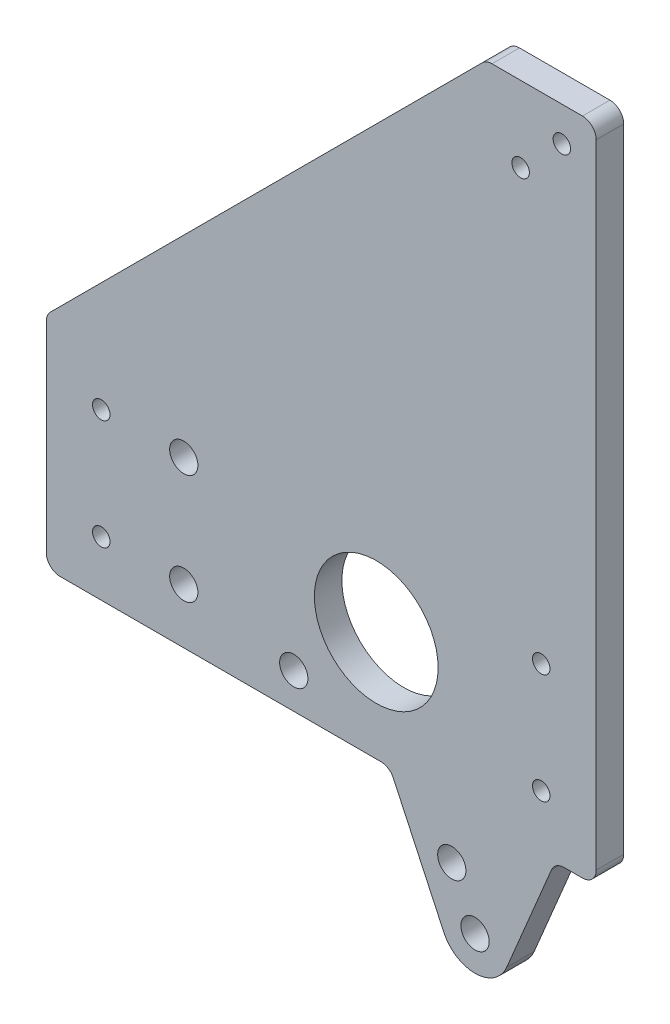
SolidWorks part; units mm, degrees
material "6061 Alloy"
ref_plane "Front Plane" through (0, 0, 0) normal (0, 0, 1) x (1, 0, 0)
ref_plane "Top Plane" through (0, 0, 0) normal (0, 1, 0) x (1, 0, 0)
ref_plane "Right Plane" through (0, 0, 0) normal (1, 0, 0) x (0, 0, -1)
sketch "Sketch1" plane through (0, 0, 0) normal (0, 0, 1) x (1, 0, 0)
  line L0 (-12.7, -76.2) -> (-26.2558, -76.2) construction
  line L1 (-12.7, -76.2) -> (12.7, -76.2) construction
  line L2 (-12.7, -76.2) -> (-12.7, 76.2) construction
  line L3 (-12.7, 76.2) -> (12.7, 76.2)
  line L4 (12.7, -76.2) -> (12.7, 76.2)
  line L5 (-12.7, -76.2) -> (12.7, 76.2) construction
  line L6 (-12.7, 76.2) -> (12.7, -76.2) construction
  line L7 (-114.3, -76.2) -> (-114.3, -25.4)
  line L8 (-12.7, 76.2) -> (-114.3, -25.4)
  line L9 (-38.1, -76.2) -> (-38.1, -50.8) construction
  line L10 (-38.1, -50.8) -> (12.7, -50.8) construction
  line L11 (-38.1, -50.8) -> (-15.2892, -99.718) construction
  line L12 (12.7, -76.2) -> (-7.9687, -102.7863) construction
  line L13 (-22.483, -103.0725) -> (-35.0138, -76.2)
  line L14 (-35.0138, -76.2) -> (-114.3, -76.2)
  line L15 (-7.9687, -102.7863) -> (3.175, -76.2)
  line L16 (3.175, -76.2) -> (12.7, -76.2)
  circle A0 centre (-15.2892, -99.718) radius 3.2639
  circle A1 centre (-20.6564, -88.2079) radius 3.2639
  arc A2 (-7.9687, -102.7863) -> (-22.483, -103.0725) centre (-15.2892, -99.718) cw
  point P0 (0, 0)
  dimension "D9" = 12.7
  dimension "D10" = 6.5278
  dimension "D11" = 6.5278
  dimension "D12" = 7.9375
  dimension "D1" = 25.4
  dimension "D2" = 152.4
  dimension "D3" = 101.6
  dimension "D4" = 50.8
  dimension "D5" = 25.4
  dimension "D6" = 50.8
  dimension "D7" = 65
  dimension "D8" = 53.975
  dimension "D13" = 65
  dimension "D14" = 9.525
extrude "Boss-Extrude1" add sketch "Sketch1" along normal blind 6.35
sketch "Sketch2" plane through (0, 0, 6.35) normal (0, 0, 1) x (1, 0, 0)
  line L1 (12.7, 76.2) -> (4.7625, 76.2) construction
  line L2 (12.7, 76.2) -> (12.7, 68.2625) construction
  line L3 (12.7, 68.2625) -> (4.7625, 68.2625) construction
  line L4 (4.7625, 76.2) -> (4.7625, 68.2625) construction
  line L5 (12.7, 76.2) -> (-4.7625, 76.2) construction
  line L6 (12.7, 76.2) -> (12.7, 58.7375) construction
  line L7 (12.7, 58.7375) -> (-4.7625, 58.7375) construction
  line L8 (-4.7625, 76.2) -> (-4.7625, 58.7375) construction
  circle A0 centre (4.7625, 68.2625) radius 2.0193
  circle A1 centre (-4.7625, 58.7375) radius 2.0193
  dimension "D3" = 4.0386
  dimension "D6" = 4.0386
  dimension "D1" = 7.9375
  dimension "D2" = 7.9375
  dimension "D4" = 17.4625
  dimension "D5" = 17.4625
extrude "Cut-Extrude1" cut sketch "Sketch2" against normal blind 6.35
sketch "Sketch3" plane through (0, 0, 6.35) normal (0, 0, 1) x (1, 0, 0)
  line L0 (0, -63.5) -> (0, -38.1) construction
  line L1 (12.7, -76.2) -> (0, -76.2) construction
  line L2 (12.7, -76.2) -> (12.7, -63.5) construction
  line L3 (12.7, -63.5) -> (0, -63.5) construction
  line L4 (0, -76.2) -> (0, -63.5) construction
  circle A0 centre (0, -63.5) radius 2.0193
  circle A1 centre (0, -38.1) radius 2.0193
  dimension "D3" = 4.0386
  dimension "D5" = 4.0386
  dimension "D1" = 12.7
  dimension "D2" = 12.7
  dimension "D4" = 25.4
extrude "Cut-Extrude2" cut sketch "Sketch3" against normal blind 6.35
sketch "Sketch5" plane through (0, 0, 6.35) normal (0, 0, 1) x (1, 0, 0)
  line L0 (-101.6, -63.5) -> (-101.6, -38.1) construction
  line L1 (-114.3, -76.2) -> (-101.6, -76.2) construction
  line L2 (-114.3, -76.2) -> (-114.3, -63.5) construction
  line L3 (-114.3, -63.5) -> (-101.6, -63.5) construction
  line L4 (-101.6, -76.2) -> (-101.6, -63.5) construction
  circle A0 centre (-101.6, -63.5) radius 2.0193
  circle A1 centre (-101.6, -38.1) radius 2.0193
  dimension "D3" = 4.0386
  dimension "D5" = 4.0386
  dimension "D1" = 12.7
  dimension "D2" = 12.7
  dimension "D4" = 25.4
extrude "Cut-Extrude3" cut sketch "Sketch5" against normal blind 6.35
sketch "Sketch6" plane through (0, 0, 6.35) normal (0, 0, 1) x (1, 0, 0)
  line L0 (12.7, -76.2) -> (12.7, 76.2) construction
  line L2 (-114.3, -76.2) -> (-35.0138, -76.2) construction
  circle A0 centre (-38.1, -50.8) radius 14.2875
  dimension "D3" = 28.575
  dimension "D2" = 25.4
  dimension "D1" = 50.8
extrude "Cut-Extrude4" cut sketch "Sketch6" against normal through all
sketch "Sketch7" plane through (0, 0, 6.35) normal (0, 0, 1) x (1, 0, 0)
  line L0 (-38.1, -50.8) -> (-57.15, -50.8) construction
  line L1 (-57.15, -50.8) -> (-57.15, -64.77) construction
  line L2 (-57.15, -68.0339) -> (-57.15, -64.77) construction
  circle A0 centre (-57.15, -68.0339) radius 3.2639
  dimension "D3" = 6.5278
  dimension "D1" = 19.05
  dimension "D2" = 13.97
extrude "Cut-Extrude5" cut sketch "Sketch7" against normal through all
hole_wizard "F (0.257) Diameter Hole1" positions "Sketch8" profile "Sketch9" hole size "F" standard "ANSI Inch" end condition through all
sketch "Sketch8" plane through (0, 0, 6.35) normal (0, 0, 1) x (1, 0, 0)
  line L1 (-114.3, -25.4) -> (-114.3, -76.2) construction
  line L2 (-114.3, -76.2) -> (-35.0138, -76.2) construction
  point P0 (-82.55, -38.1)
  point P2 (-82.55, -63.5)
  dimension "D1" = 25.4
  dimension "D2" = 12.7
  dimension "D3" = 31.75
sketch "Sketch9" plane through (-82.55, -38.1, 6.35) normal (1, 0, 0) x (0, -1, 0)
  line L0 (0, 0) -> (0, 6.35)
  line L1 (0, 6.35) -> (3.2639, 6.35)
  line L2 (3.2639, 6.35) -> (3.2639, 0)
  line L5 (3.2639, 0) -> (0, 0)
  line L11 (0, -6.35) -> (0, 107.95) construction
  dimension "Thru Hole Dia." = 6.5278
  dimension "Thru Hole Depth" = 6.35
sketch "Sketch10" plane through (0, 0, 6.35) normal (0, 0, 1) x (1, 0, 0)
  line L0 (-114.3, -25.4) -> (-105.3197, -25.4) construction
  line L1 (-99.8997, -19.9799) -> (-63.5, 16.4197)
  line L2 (-59.0099, 16.4197) -> (-22.6102, -19.9799)
  line L3 (-24.8553, -25.4) -> (-97.6546, -25.4)
  line L4 (-12.7, 76.2) -> (-12.7, -25.4) construction
  line L5 (-12.7, -25.4) -> (-63.5, 25.4) construction
  line L6 (-12.7, 76.2) -> (-114.3, -25.4) construction
  line L7 (-17.1901, -25.4) -> (-12.7, -25.4) construction
  line L8 (-12.7, -13.2447) -> (-12.7, 59.5546)
  line L9 (-18.1201, 61.7997) -> (-54.5197, 25.4)
  line L10 (-54.5197, 20.9099) -> (-18.1201, -15.4898)
  line L11 (-5.4201, 44.6096) -> (0.9299, 50.9596)
  line L12 (6.35, 48.7145) -> (6.35, -25.8033)
  line L13 (0.0137, -26.0978) -> (-6.3363, 42.07)
  line L14 (12.7, -76.2) -> (12.7, 76.2) construction
  line L15 (4.7625, 68.2625) -> (-4.7625, 58.7375) construction
  line L16 (-73.025, -34.925) -> (-73.025, -66.675)
  line L17 (-66.8776, -67.7911) -> (-54.9555, -36.0411)
  line L18 (-57.9279, -31.75) -> (-69.85, -31.75)
  line L19 (-114.3, -76.2) -> (-35.0138, -76.2) construction
  arc A0 (6.35, -25.8033) -> (0.0137, -26.0978) centre (3.175, -25.8033) cw
  arc A1 (0.9299, 50.9596) -> (6.35, 48.7145) centre (3.175, 48.7145) cw
  arc A2 (-5.4201, 44.6096) -> (-6.3363, 42.07) centre (-3.175, 42.3645) ccw
  arc A3 (-97.6546, -25.4) -> (-99.8997, -19.9799) centre (-97.6546, -22.225) cw
  arc A4 (-22.6102, -19.9799) -> (-24.8553, -25.4) centre (-24.8553, -22.225) cw
  arc A5 (-63.5, 16.4197) -> (-59.0099, 16.4197) centre (-61.2549, 14.1747) cw
  arc A6 (-54.5197, 25.4) -> (-54.5197, 20.9099) centre (-52.2747, 23.1549) ccw
  arc A7 (-12.7, -13.2447) -> (-18.1201, -15.4898) centre (-15.875, -13.2447) cw
  arc A8 (-12.7, 59.5546) -> (-18.1201, 61.7997) centre (-15.875, 59.5546) ccw
  circle A9 centre (-4.7625, 58.7375) radius 2.0193 construction
  arc A10 (-73.025, -66.675) -> (-66.8776, -67.7911) centre (-69.85, -66.675) ccw
  arc A11 (-54.9555, -36.0411) -> (-57.9279, -31.75) centre (-57.9279, -34.925) ccw
  arc A12 (-73.025, -34.925) -> (-69.85, -31.75) centre (-69.85, -34.925) cw
  circle A13 centre (-82.55, -38.1) radius 3.2639 construction
  circle A14 centre (-38.1, -50.8) radius 14.2875 construction
  circle A17 centre (0, -38.1) radius 2.0193 construction
  point P36 (-12.7, -20.9099)
  point P39 (-12.7, 67.2197)
  dimension "D1" = 3.175
  dimension "D7" = 9.525
  dimension "D9" = 3.175
  dimension "D12" = 25.4
  dimension "D13" = 9.525
  dimension "D14" = 12.7
  dimension "D2" = 6.35
  dimension "D3" = 6.35
  dimension "D4" = 3.175
  dimension "D5" = 6.35
  dimension "D6" = 9.525
  dimension "D8" = 6.35
  dimension "D10" = 6.35
  dimension "D11" = 9.525
extrude "Cut-Extrude6" [suppressed] cut sketch "Sketch10" against normal blind 4.7625
fillet "Fillet1" radius 3.175 3 edges at (-35.0138, -76.2, 3.175) (12.7, -76.2, 3.175) (3.175, -76.2, 3.175)
fillet "Fillet2" radius 3.175 4 edges at (-114.3, -76.2, 3.175) (-114.3, -25.4, 3.175) (12.7, 76.2, 3.175) (-12.7, 76.2, 3.175)
